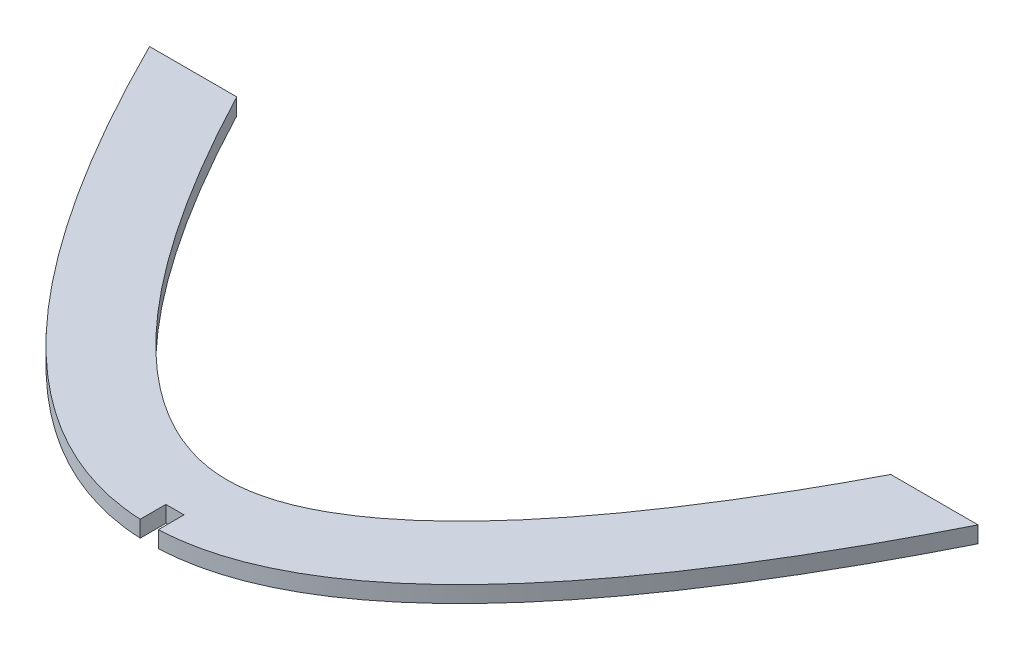
SolidWorks part; units mm, degrees
ref_plane "Front Plane" through (0, 0, 0) normal (0, 0, 1) x (1, 0, 0)
ref_plane "Top Plane" through (0, 0, 0) normal (0, 1, 0) x (1, 0, 0)
ref_plane "Right Plane" through (0, 0, 0) normal (1, 0, 0) x (0, 0, -1)
sketch "Sketch1" plane through (0, 0, 0) normal (0, 1, 0) x (1, 0, 0)
  line L0 (-80, 80) -> (-63.1533, 80)
  line L1 (63.1533, 80) -> (80, 80)
  spline S0 degree 2 poles (-90.0959, 101.4658) (0, -101.4658) (90.0959, 101.4658) knots 0 0 0 1 1 1 construction
  spline S1 degree 2 poles (-80, 80) (0, -80) (80, 80) knots 0.056028 0.056028 0.056028 0.943972 0.943972 0.943972
  spline S2 degree 1 poles (-66.5836, 86.7082) (66.5836, 86.7082) knots 0 0 1 1 construction
  spline S3 degree 3 poles (-66.5836, 86.7082) (-66.1837, 85.9084) (-65.3748, 84.3032) (-63.7692, 81.1675) (-61.7632, 77.3434) (-59.365, 72.9219) (-56.1781, 67.2454) (-52.2176, 60.5632) (-47.5101, 53.2091) (-42.8576, 46.5233) (-36.745, 38.5032) (-29.3112, 30.1609) (-20.884, 22.8243) (-13.153, 18.0421) (-6.2547, 15.5059) (0, 14.747) (6.2547, 15.5059) (13.153, 18.0421) (20.884, 22.8243) (29.3112, 30.1609) (36.745, 38.5032) (42.8576, 46.5233) (47.5101, 53.2091) (52.2176, 60.5632) (56.1781, 67.2454) (59.365, 72.9219) (61.7632, 77.3434) (63.7692, 81.1675) (65.3748, 84.3032) (66.1837, 85.9084) (66.5836, 86.7082) knots 0.056028 0.056028 0.056028 0.056028 0.062965 0.069903 0.083777 0.097651 0.111525 0.139273 0.167021 0.19477 0.222518 0.278014 0.333511 0.389007 0.444504 0.5 0.555496 0.610993 0.666489 0.721986 0.777482 0.80523 0.832979 0.860727 0.888475 0.902349 0.916223 0.930097 0.937035 0.943972 0.943972 0.943972 0.943972 only from (-63.1533, 80) to (63.1533, 80)
  dimension "D1" = 15
extrude "Boss-Extrude2" add sketch "Sketch1" along normal blind 3.175 contours S3 L0 S1 L1
sketch "Sketch2" plane through (0, 3.175, 0) normal (0, 1, 0) x (1, 0, 0)
  line L1 (-1.8381, 5) -> (1.6619, 5)
  line L2 (-1.8381, 5) -> (-1.8381, 0)
  line L3 (-1.8381, 0) -> (1.6619, 0)
  line L4 (1.6619, 5) -> (1.6619, 0)
  dimension "D1" = 5
  dimension "D2" = 3.5
extrude "Cut-Extrude1" cut sketch "Sketch2" against normal through all
